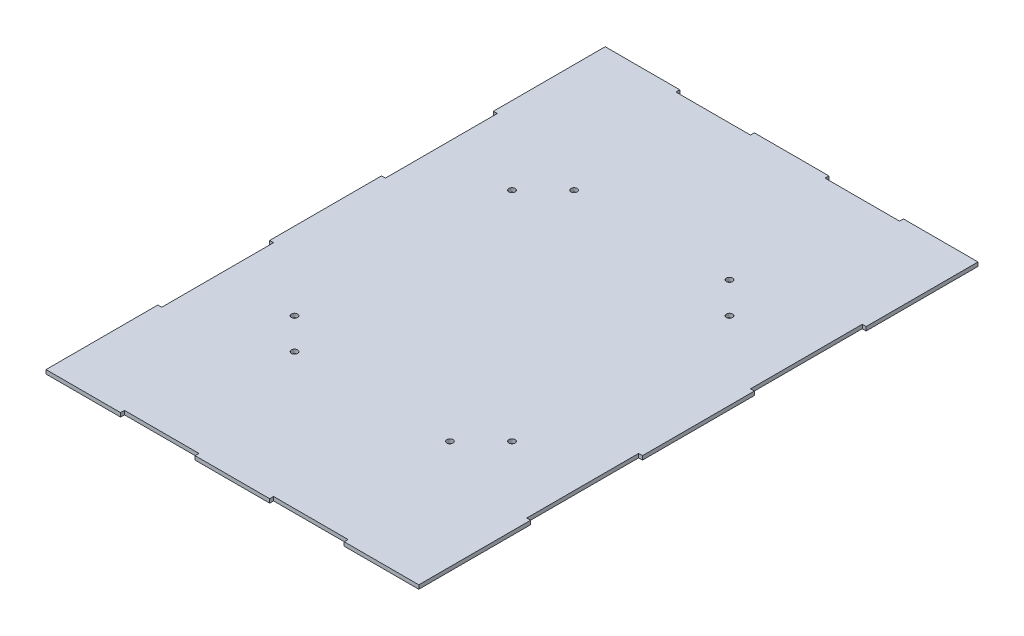
SolidWorks part; units mm, degrees
ref_plane "Front Plane" through (0, 0, 0) normal (0, 0, 1) x (1, 0, 0)
ref_plane "Top Plane" through (0, 0, 0) normal (0, 1, 0) x (1, 0, 0)
ref_plane "Right Plane" through (0, 0, 0) normal (1, 0, 0) x (0, 0, -1)
sketch "Sketch1" plane through (0, 0, 0) normal (0, 1, 0) x (1, 0, 0)
  line L1 (152.4, -228.6) -> (-152.4, -228.6)
  line L2 (152.4, -228.6) -> (152.4, 228.6)
  line L3 (152.4, 228.6) -> (-152.4, 228.6)
  line L4 (-152.4, -228.6) -> (-152.4, 228.6)
  line L5 (152.4, -228.6) -> (-152.4, 228.6) construction
  line L6 (152.4, 228.6) -> (-152.4, -228.6) construction
  point P0 (0, 0)
  dimension "D1" = 457.2
extrude "Boss-Extrude1" add sketch "Sketch1" along normal blind 3.175
sketch "Sketch3" plane through (0, 3.175, 0) normal (0, 1, 0) x (1, 0, 0)
  line L0 (-91.44, 228.6) -> (-30.48, 228.6)
  line L1 (-91.44, -225.425) -> (-30.48, -225.425)
  line L2 (-91.44, -225.425) -> (-91.44, -228.6)
  line L3 (-91.44, -228.6) -> (-30.48, -228.6)
  line L4 (-30.48, -225.425) -> (-30.48, -228.6)
  line L5 (-152.4, -228.6) -> (152.4, -228.6) construction
  line L6 (30.48, -228.6) -> (91.44, -228.6)
  line L7 (30.48, -228.6) -> (30.48, -225.425)
  line L8 (30.48, -225.425) -> (91.44, -225.425)
  line L9 (91.44, -228.6) -> (91.44, -225.425)
  line L10 (-30.48, 228.6) -> (-30.48, 225.425)
  line L11 (30.48, 228.6) -> (91.44, 228.6)
  line L12 (30.48, 225.425) -> (30.48, 228.6)
  line L13 (91.44, 225.425) -> (91.44, 228.6)
  line L14 (-91.44, 228.6) -> (-91.44, 225.425)
  line L15 (-91.44, 225.425) -> (-30.48, 225.425)
  line L16 (-152.4, 228.6) -> (-152.4, -228.6) construction
  line L17 (30.48, 225.425) -> (91.44, 225.425)
  line L18 (152.4, 45.72) -> (149.225, 45.72)
  line L19 (152.4, -137.16) -> (152.4, -45.72)
  line L20 (152.4, 137.16) -> (149.225, 137.16)
  line L21 (152.4, 45.72) -> (152.4, 137.16)
  line L22 (149.225, -137.16) -> (152.4, -137.16)
  line L23 (149.225, 45.72) -> (149.225, 137.16)
  line L24 (149.225, -45.72) -> (152.4, -45.72)
  line L25 (149.225, -137.16) -> (149.225, -45.72)
  line L29 (-152.4, 228.6) -> (-152.4, -228.6) construction
  line L30 (152.4, -228.6) -> (152.4, 228.6) construction
  line L31 (152.4, -228.6) -> (152.4, 228.6) construction
  line L34 (-149.225, 137.16) -> (-152.4, 137.16)
  line L35 (-152.4, -45.72) -> (-149.225, -45.72)
  line L36 (-149.225, 45.72) -> (-149.225, 137.16)
  line L37 (-152.4, -137.16) -> (-149.225, -137.16)
  line L38 (-149.225, 45.72) -> (-152.4, 45.72)
  line L39 (-152.4, -137.16) -> (-152.4, -45.72)
  line L40 (-149.225, -137.16) -> (-149.225, -45.72)
  line L41 (-152.4, 45.72) -> (-152.4, 137.16)
  circle A0 centre (-63.5, -114.3) radius 2.54
  circle A1 centre (-88.9, -88.9) radius 2.54
  circle A2 centre (88.9, -88.9) radius 2.54
  circle A3 centre (63.5, -114.3) radius 2.54
  circle A4 centre (63.5, 114.3) radius 2.54
  circle A5 centre (88.9, 88.9) radius 2.54
  circle A6 centre (-88.9, 88.9) radius 2.54
  circle A7 centre (-63.5, 114.3) radius 2.54
  dimension "D14" = 0
  dimension "D2" = 0
  dimension "D3" = 3.175
  dimension "D4" = 0
  dimension "D5" = 60.96
  dimension "D6" = 60.96
  dimension "D7" = 3.175
  dimension "D8" = 91.44
  dimension "D9" = 3.175
  dimension "D10" = 91.44
  dimension "D11" = 60.96
  dimension "D12" = 3.175
  dimension "D13" = 91.44
  dimension "D15" = 0
  dimension "D16" = 60.96
  dimension "D17" = 60.96
  dimension "D18" = 60.96
  dimension "D19" = 60.96
  dimension "D20" = 114.3
  dimension "D21" = 228.6
  dimension "D22" = 127
  dimension "D23" = 25.4
  dimension "D24" = 25.4
  dimension "D25" = 25.4
  dimension "D26" = 25.4
extrude "Cut-Extrude1" cut sketch "Sketch3" against normal blind 6.35
equation "\"SideLength\"= 18"
equation "\"D1@Sketch1\"=\"SideLength\""
equation "\"thick\"=0.125"
equation "\"D3@Sketch3\" = \"thick\""
equation "\"D7@Sketch3\"=\"thick\""
